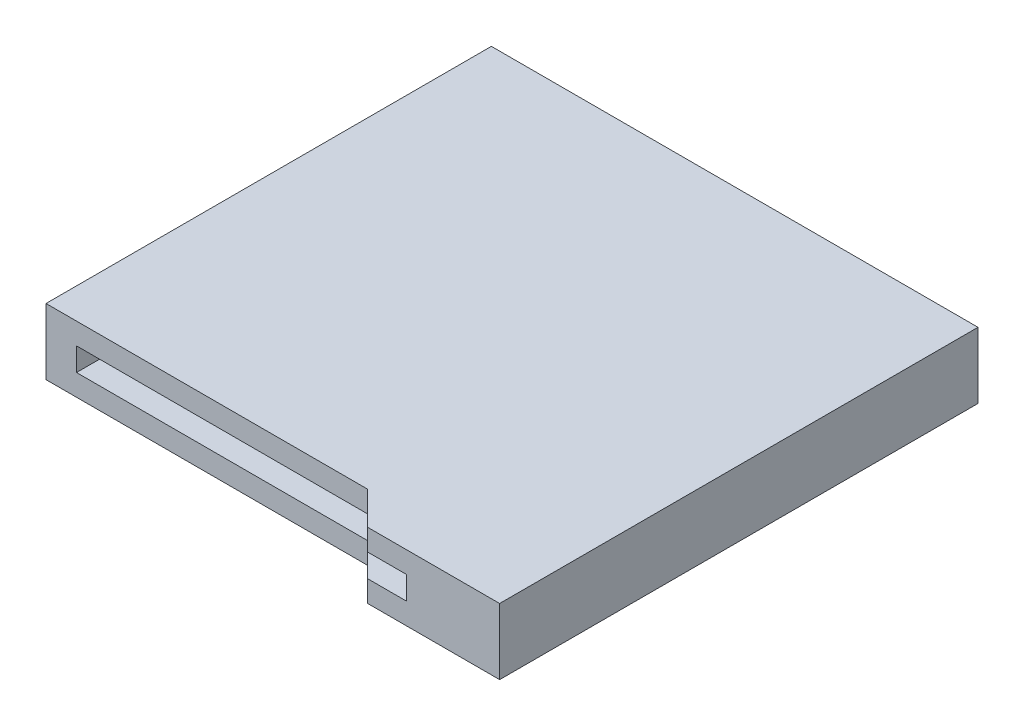
SolidWorks part; units mm, degrees
ref_plane "Front Plane" through (0, 0, 0) normal (0, 0, 1) x (1, 0, 0)
ref_plane "Top Plane" through (0, 0, 0) normal (0, 1, 0) x (1, 0, 0)
ref_plane "Right Plane" through (0, 0, 0) normal (1, 0, 0) x (0, 0, -1)
sketch "Sketch1" plane through (0, 0, 0) normal (0, 1, 0) x (1, 0, 0)
  line L1 (-7.375, 7.25) -> (7.375, 7.25)
  line L2 (-7.375, 7.25) -> (-7.375, -7.25)
  line L3 (-7.375, -7.25) -> (7.375, -7.25)
  line L4 (7.375, 7.25) -> (7.375, -7.25)
  line L5 (-7.375, 7.25) -> (7.375, -7.25) construction
  line L6 (-7.375, -7.25) -> (7.375, 7.25) construction
  point P0 (0, 0)
  dimension "D1" = 14.5
  dimension "D2" = 14.75
extrude "Boss-Extrude1" add sketch "Sketch1" along normal blind 2
sketch "Sketch2" plane through (0, 2, 0) normal (0, 1, 0) x (1, 0, 0)
  line L0 (-7.375, -6.25) -> (2.375, -6.25)
  line L1 (-7.375, 7.25) -> (-7.375, -7.25) construction
  line L2 (2.375, -6.25) -> (3.375, -7.25)
  line L3 (-7.375, -7.25) -> (7.375, -7.25) construction
  line L4 (3.375, -7.25) -> (-7.375, -7.25)
  line L5 (-7.375, -7.25) -> (-7.375, -6.25)
  dimension "D1" = 1
  dimension "D2" = 4
  dimension "D3" = 135
extrude "Cut-Extrude1" cut sketch "Sketch2" against normal blind 2
sketch "Sketch3" plane through (0, 0, 7.25) normal (0, 0, 1) x (1, 0, 0)
  line L0 (-0.95, 0) -> (-0.95, 2) construction
  line L1 (-6.45, 1.35) -> (4.55, 1.35)
  line L2 (-6.45, 1.35) -> (-6.45, 0.65)
  line L3 (-6.45, 0.65) -> (4.55, 0.65)
  line L4 (4.55, 1.35) -> (4.55, 0.65)
  line L5 (-6.45, 1.35) -> (4.55, 0.65) construction
  line L6 (-6.45, 0.65) -> (4.55, 1.35) construction
  line L7 (2.375, 0) -> (-7.375, 0) construction
  line L8 (2.375, 2) -> (-7.375, 2) construction
  point P0 (-0.95, 1)
  point P11 (-0.95, 1)
  dimension "D1" = 11
  dimension "D2" = 0.7
  dimension "D3" = 0.95
extrude "Cut-Extrude2" cut sketch "Sketch3" against normal blind 12
sketch "Sketch4" plane through (0, 0, 0) normal (0, -1, 0) x (1, 0, 0)
  line L0 (0, 0) -> (0, -7.25) construction
  line L1 (7.375, -7.25) -> (-7.375, -7.25) construction
  line L2 (0, 3.25) -> (-4.95, 3.25) construction
  line L3 (0, 3.25) -> (3.05, 3.25) construction
  circle A0 centre (-4.95, 3.25) radius 0.4
  circle A1 centre (3.05, 3.25) radius 0.4
  dimension "D2" = 0.8
  dimension "D1" = 8
  dimension "D3" = 10.5
  dimension "D4" = 4.95
extrude "Boss-Extrude2" add sketch "Sketch4" along normal blind 0.65
